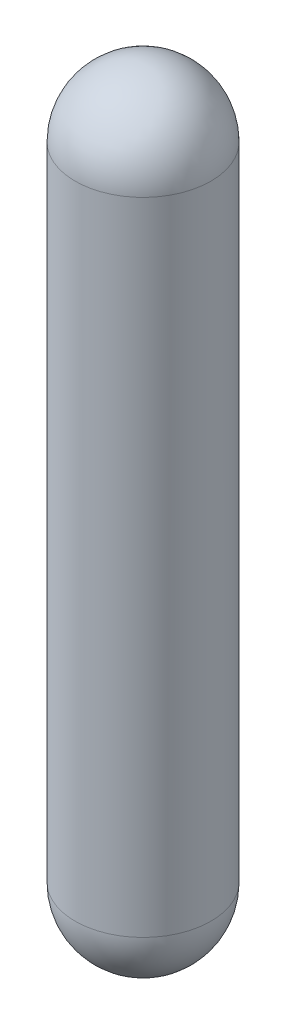
SolidWorks part; units mm, degrees
ref_plane "Front Plane" through (0, 0, 0) normal (0, 0, 1) x (1, 0, 0)
ref_plane "Top Plane" through (0, 0, 0) normal (0, 1, 0) x (1, 0, 0)
ref_plane "Right Plane" through (0, 0, 0) normal (1, 0, 0) x (0, 0, -1)
sketch "Sketch1" plane through (0, 0, 0) normal (0, 0, 1) x (1, 0, 0)
  line L0 (0, 0) -> (0, 85.3836) construction
  line L1 (9.0483, 85.3836) -> (9.0483, 0)
  line L3 (0, 94.4318) -> (0, -9.0483)
  arc A0 (9.0483, 85.3836) -> (0, 94.4318) centre (0, 85.3836) ccw
  arc A1 (0, -9.0483) -> (9.0483, 0) centre (0, 0) ccw
revolve "Revolve1" add sketch "Sketch1" angle 360 about L0
